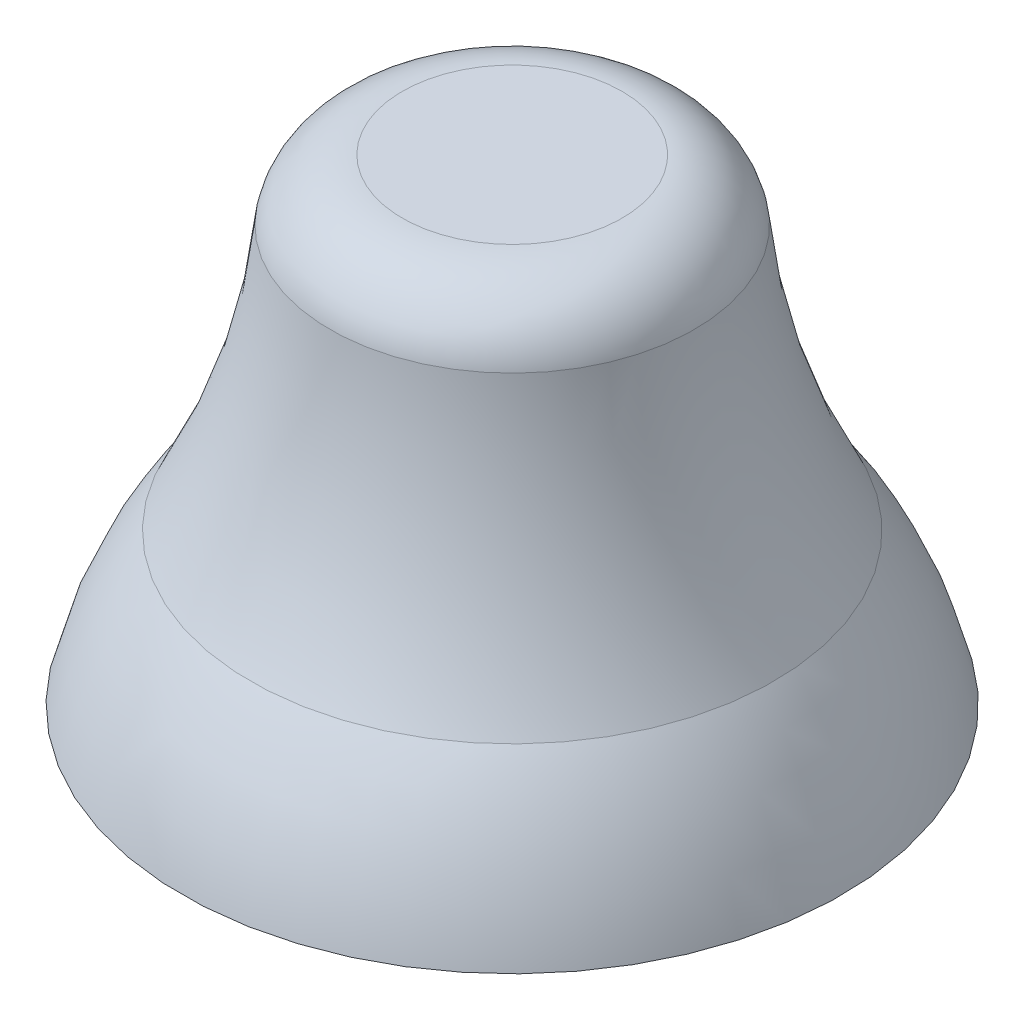
SolidWorks part; units mm, degrees
ref_plane "Front Plane" through (0, 0, 0) normal (0, 0, 1) x (1, 0, 0)
ref_plane "Top Plane" through (0, 0, 0) normal (0, 1, 0) x (1, 0, 0)
ref_plane "Right Plane" through (0, 0, 0) normal (1, 0, 0) x (0, 0, -1)
sketch "Sketch1" plane through (0, 0, 0) normal (0, 0, 1) x (1, 0, 0)
  line L0 (0, 0) -> (0.9, 0)
  line L1 (0, 0) -> (0, 1.3)
  line L2 (0, 1.3) -> (0.3, 1.3)
  arc A0 (0.9, 0) -> (0.714, 0.412) centre (-0.1742, -0.237) ccw
  arc A1 (0.714, 0.412) -> (0.4969, 1.135) centre (2.3889, 1.309) cw
  arc A2 (0.4969, 1.135) -> (0.3, 1.3) centre (0.3, 1.1) ccw
  dimension "D3" = 0.2
  dimension "D4" = 1.1
  dimension "D5" = 1.9
  dimension "D1" = 1.3
  dimension "D2" = 0.9
  dimension "D6" = 0.3
  dimension "D7" = 0.2
  dimension "D8" = 0.165
  dimension "D9" = 0.888
  dimension "D10" = 0.714
revolve "Revolve1" add sketch "Sketch1" angle 360 about L1
